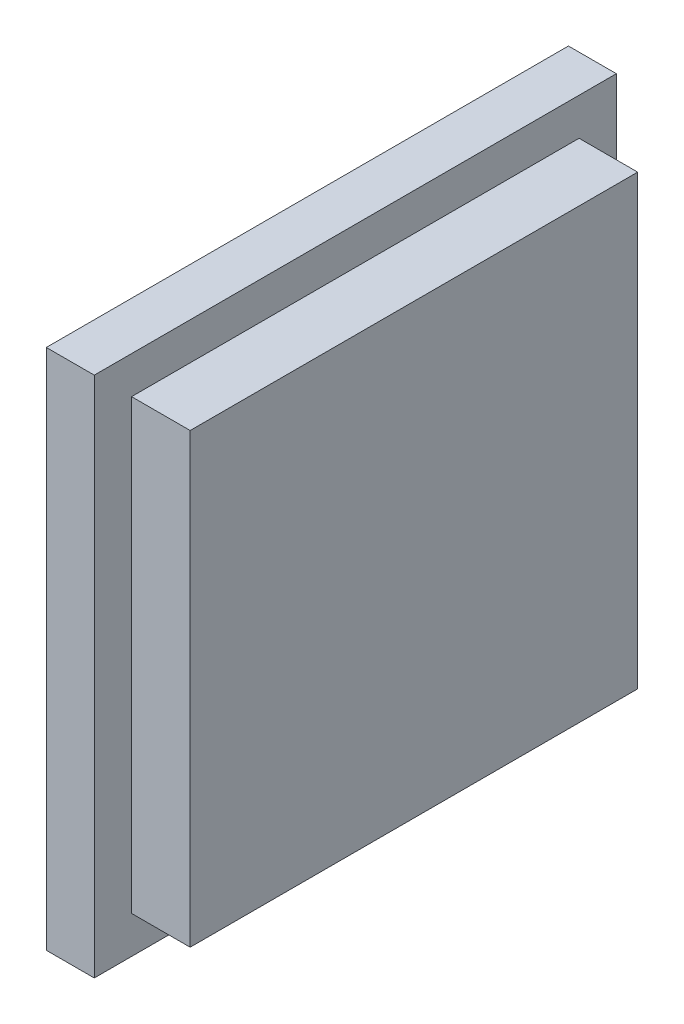
SolidWorks part; units mm, degrees
ref_plane "Front Plane" through (0, 0, 0) normal (0, 0, 1) x (1, 0, 0)
ref_plane "Top Plane" through (0, 0, 0) normal (0, 1, 0) x (1, 0, 0)
ref_plane "Right Plane" through (0, 0, 0) normal (1, 0, 0) x (0, 0, -1)
sketch "Sketch1" plane through (0, 0, 0) normal (1, 0, 0) x (0, 0, -1)
  line L1 (24.5, 24.5) -> (-24.5, 24.5)
  line L2 (24.5, 24.5) -> (24.5, -24.5)
  line L3 (24.5, -24.5) -> (-24.5, -24.5)
  line L4 (-24.5, 24.5) -> (-24.5, -24.5)
  line L5 (24.5, 24.5) -> (-24.5, -24.5) construction
  line L6 (24.5, -24.5) -> (-24.5, 24.5) construction
  point P0 (0, 0)
  dimension "D1" = 49
  dimension "D2" = 49
extrude "Boss-Extrude1" add sketch "Sketch1" along normal blind 4.5
sketch "Sketch3" plane through (4.5, 0, 0) normal (1, 0, 0) x (0, 0, -1)
  line L0 (24.5, 24.5) -> (-24.5, 24.5) construction
  line L1 (-21, 21) -> (21, 21)
  line L2 (-21, 21) -> (-21, -21)
  line L3 (-21, -21) -> (21, -21)
  line L4 (21, 21) -> (21, -21)
  line L5 (-21, 21) -> (21, -21) construction
  line L6 (-21, -21) -> (21, 21) construction
  line L7 (-24.5, 24.5) -> (-24.5, -24.5) construction
  point P0 (0, 0)
  dimension "D1" = 3.5
  dimension "D2" = 3.5
extrude "Boss-Extrude3" add sketch "Sketch3" along normal blind 5.5
